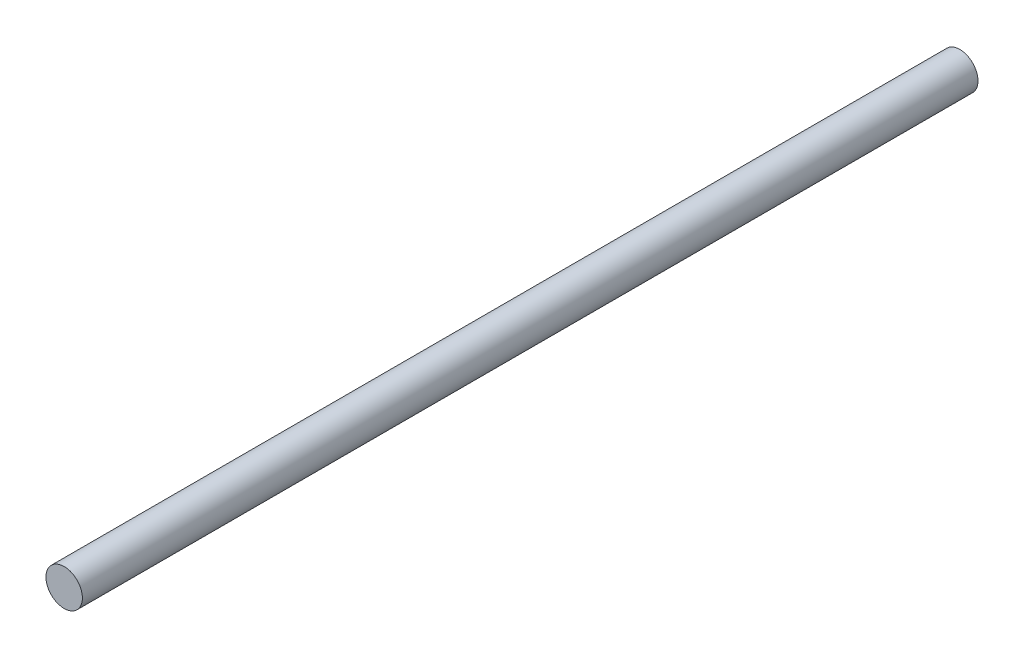
SolidWorks part; units mm, degrees
ref_plane "Face" through (0, 0, 0) normal (0, 0, 1) x (1, 0, 0)
ref_plane "Dessus" through (0, 0, 0) normal (0, 1, 0) x (1, 0, 0)
ref_plane "Droite" through (0, 0, 0) normal (1, 0, 0) x (0, 0, -1)
sketch "Esquisse1" plane through (0, 0, 0) normal (0, 0, 1) x (1, 0, 0)
  circle A0 centre (0, 0) radius 2.5
  dimension "D1" = 5
extrude "Extrusion1" add sketch "Esquisse1" along normal blind 123
